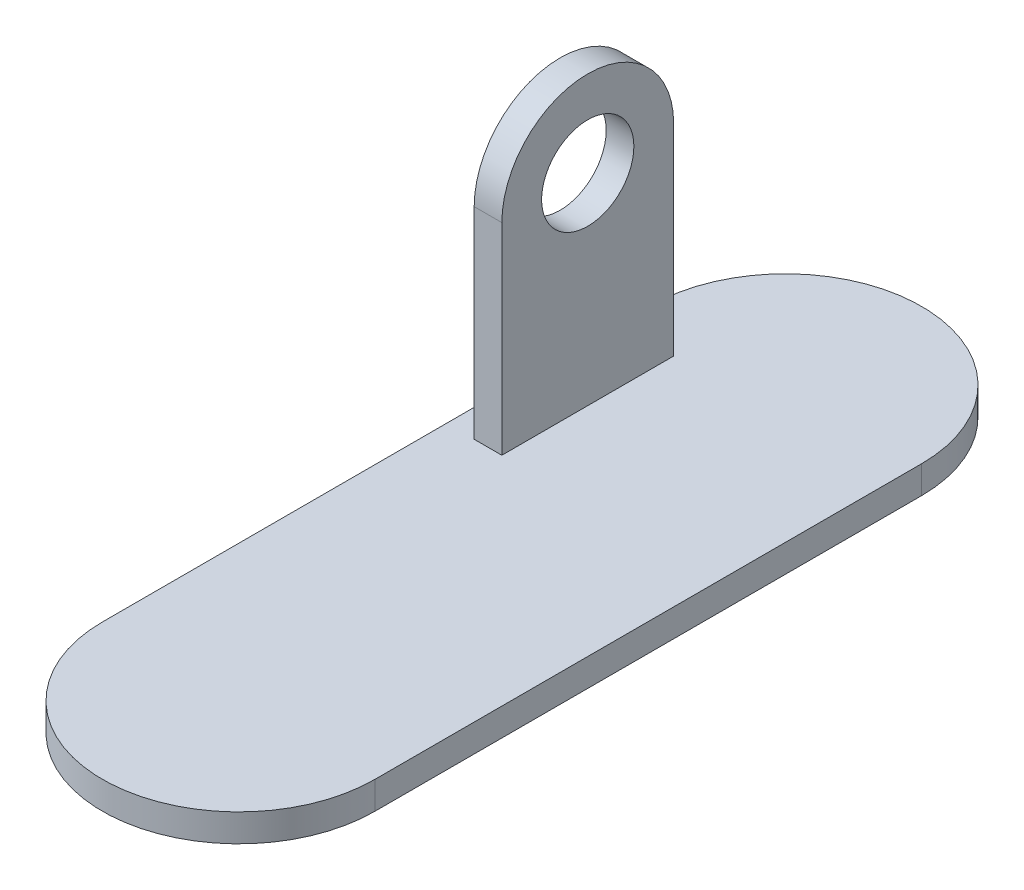
SolidWorks part; units mm, degrees
ref_plane "Front Plane" through (0, 0, 0) normal (0, 0, 1) x (1, 0, 0)
ref_plane "Top Plane" through (0, 0, 0) normal (0, 1, 0) x (1, 0, 0)
ref_plane "Right Plane" through (0, 0, 0) normal (1, 0, 0) x (0, 0, -1)
sketch "Sketch1" plane through (0, 0, 0) normal (0, 1, 0) x (1, 0, 0)
  line L0 (0, -88.9) -> (0, 88.9) construction
  line L2 (44.323, 88.9) -> (44.323, -88.9)
  line L3 (0, 0) -> (-26.323, 0) construction
  line L14 (-44.323, 88.9) -> (-44.323, -88.9)
  arc A0 (44.323, 88.9) -> (-44.323, 88.9) centre (0, 88.9) ccw
  arc A1 (-44.323, -88.9) -> (44.323, -88.9) centre (0, -88.9) ccw
  point P8 (0, 0)
  point P13 (-89.4761, 0)
  point P18 (-35.323, 0)
  dimension "D2" = 88.646
  dimension "D1" = 177.8
extrude "Boss-Extrude1" add sketch "Sketch1" along normal blind 9
sketch "Sketch2" plane through (0, 9, 0) normal (0, 1, 0) x (1, 0, 0)
  line L0 (-44.323, 88.9) -> (-44.323, -88.9) construction
  line L1 (-35.323, 78.9) -> (-26.323, 78.9)
  line L2 (-35.323, 78.9) -> (-35.323, 23.02)
  line L3 (-35.323, 23.02) -> (-26.323, 23.02)
  line L4 (-26.323, 78.9) -> (-26.323, 23.02)
  line L5 (-44.323, 88.9) -> (44.323, 88.9) construction
  dimension "D1" = 9
  dimension "D2" = 9
  dimension "D3" = 55.88
  dimension "D4" = 10
extrude "Boss-Extrude2" add sketch "Sketch2" along normal blind 65.53
sketch "Sketch3" plane through (-26.323, 0, 0) normal (1, 0, 0) x (0, 0, -1)
  line L0 (23.02, 74.53) -> (78.9, 74.53) construction
  circle A0 centre (50.96, 74.53) radius 27.94
extrude "Boss-Extrude3" add sketch "Sketch3" against normal up to surface (9 mm away) up to face at (-35.323, 41.765, -50.96)
sketch "Sketch4" plane through (-26.323, 0, 0) normal (1, 0, 0) x (0, 0, -1)
  circle A0 centre (50.96, 74.53) radius 15
  dimension "D1" = 30
extrude "Cut-Extrude1" cut sketch "Sketch4" against normal through all
